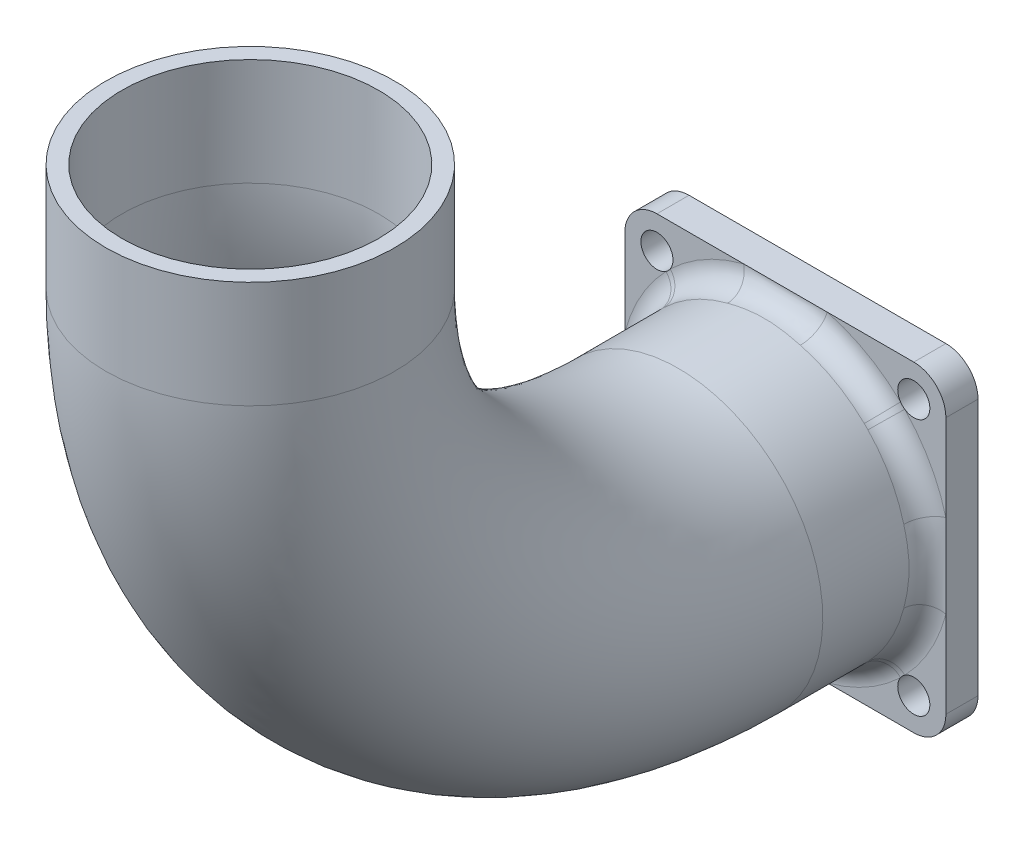
SolidWorks part; units mm, degrees
ref_plane "Plan de face" through (0, 0, 0) normal (0, 0, 1) x (1, 0, 0)
ref_plane "Plan de dessus" through (0, 0, 0) normal (0, 1, 0) x (1, 0, 0)
ref_plane "Plan de droite" through (0, 0, 0) normal (1, 0, 0) x (0, 0, -1)
sketch "Esquisse1" plane through (0, 0, 0) normal (0, 0, 1) x (1, 0, 0)
  line L1 (-15, 15) -> (15, 15)
  line L2 (-15, 15) -> (-15, -15)
  line L3 (-15, -15) -> (15, -15)
  line L4 (15, 15) -> (15, -15)
  line L5 (-15, 15) -> (15, -15) construction
  line L6 (-15, -15) -> (15, 15) construction
  circle A0 centre (0, 0) radius 12
  circle A1 centre (-12, 12) radius 1.5
  circle A2 centre (12, 12) radius 1.5
  circle A3 centre (12, -12) radius 1.5
  circle A4 centre (-12, -12) radius 1.5
  point P0 (0, 0)
  point P19 (0, 0)
  dimension "D3" = 24
  dimension "D4" = 3
  dimension "D5" = 12
  dimension "D6" = 4
  dimension "D1" = 30
  dimension "D2" = 30
extrude "Boss.-Extru.1" add sketch "Esquisse1" along normal blind 3
sketch "Esquisse2" plane through (0, 0, 0) normal (1, 0, 0) x (0, 0, -1)
  line L0 (-3, 0) -> (-13, 0)
  line L1 (-3, -15) -> (-3, 15) construction
  line L2 (-53, 40) -> (-53, 50)
  arc A0 (-53, 40) -> (-13, 0) centre (-13, 40) ccw
  point P8 (-53, 0)
  dimension "D3" = 40
  dimension "D1" = 50
  dimension "D2" = 50
sketch "Esquisse4" plane through (0, 0, 3) normal (0, 0, 1) x (1, 0, 0)
  circle A0 centre (0, 0) radius 12
  circle A1 centre (0, 0) radius 12 construction
sweep "Balayage-Mince1" add profiles "Esquisse4" path "Esquisse2" parameters "D1"=1.5
fillet "Congé1" radius 2 1 edges at (13.5, 0, 3)
fillet "Congé2" radius 3 4 edges at (-15, -15, 1.5) (15, -15, 1.5) (15, 15, 1.5) (-15, 15, 1.5)
